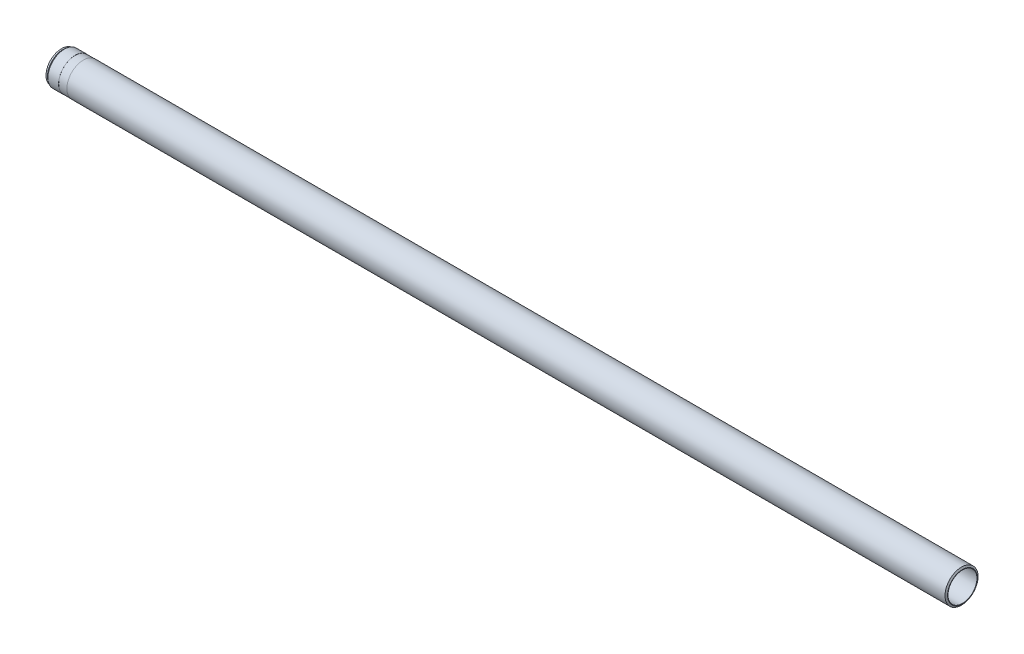
SolidWorks part; units mm, degrees
ref_plane "Front" through (0, 0, 0) normal (0, 0, 1) x (1, 0, 0)
ref_plane "Top" through (0, 0, 0) normal (0, 1, 0) x (1, 0, 0)
ref_plane "Right" through (0, 0, 0) normal (1, 0, 0) x (0, 0, -1)
sketch "Sketch1" plane through (0, 0, 0) normal (0, 0, 1) x (1, 0, 0)
  line L0 (-122.7842, 0) -> (99.5499, 0) construction
  line L1 (0, 35) -> (0, 36)
  line L2 (0, 36) -> (-2.3094, 40)
  line L3 (-2.3094, 40) -> (-2128, 40)
  line L4 (-2128, 40) -> (-2128, 39.75)
  line L5 (-2128, 39.75) -> (-2148, 39.75)
  line L6 (-2148, 39.75) -> (-2148, 40)
  line L7 (-2148, 40) -> (-2173.9296, 40)
  line L8 (-2173.9296, 40) -> (-2177.5, 37.5)
  line L9 (-2177.5, 37.5) -> (-2181, 37.5)
  line L10 (-2181, 37.5) -> (-2181, 35.7274)
  line L11 (-2181, 35.7274) -> (-2180, 35.15)
  line L12 (-2180, 35.15) -> (-2166, 35.15)
  line L13 (-2166, 35.15) -> (-2165.7402, 35)
  line L14 (-2165.7402, 35) -> (0, 35)
  dimension "D1" = 2181
  dimension "D2" = 80
  dimension "D3" = 70
  dimension "D4" = 70.3
  dimension "D5" = 75
  dimension "D6" = 72
  dimension "D7" = 60
  dimension "D8" = 79.5
  dimension "D9" = 3.5
  dimension "D10" = 35
  dimension "D11" = 30
  dimension "D12" = 1
  dimension "D13" = 30
  dimension "D14" = 15
  dimension "D15" = 33
  dimension "D16" = 20
revolve "Base-Revolve" add sketch "Sketch1" angle 360 about L0
